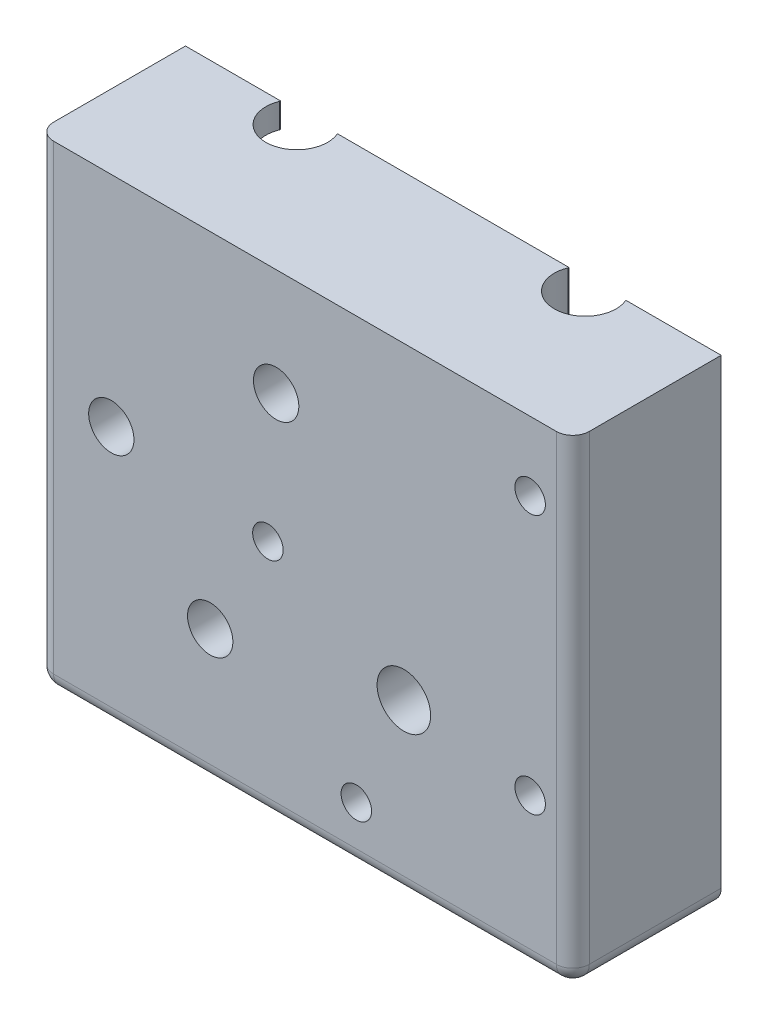
SolidWorks part; units mm, degrees
ref_plane "Front Plane" through (0, 0, 0) normal (0, 0, 1) x (1, 0, 0)
ref_plane "Top Plane" through (0, 0, 0) normal (0, 1, 0) x (1, 0, 0)
ref_plane "Right Plane" through (0, 0, 0) normal (1, 0, 0) x (0, 0, -1)
sketch "Sketch1" plane through (0, 0, 0) normal (0, 0, 1) x (1, 0, 0)
  line L28 (-44.5, 34.5) -> (-32.9789, 34.5)
  line L29 (-32.9789, 34.5) -> (-32.9789, 37.5)
  line L30 (-32.9789, 37.5) -> (-44.5, 37.5)
  line L31 (-44.5, 37.5) -> (-44.5, 34.5)
  line L32 (-26.0211, 30.5) -> (-26.0211, 5.4298)
  line L33 (-14.9652, 0.9641) -> (-7.0998, -1.4681)
  line L34 (-0.1869, 7.2476) -> (-7.1051, 19.0663)
  line L35 (-23.5, 30.5) -> (-26.0211, 30.5)
  line L36 (-26.0211, 37.5) -> (-26.0211, 34.5)
  line L37 (-26.0211, 34.5) -> (-15.5, 34.5)
  line L38 (-5.686, 22.5805) -> (2.0211, 9.414)
  line L39 (2.0211, 9.414) -> (2.0211, 37.5)
  line L40 (2.0211, 37.5) -> (-26.0211, 37.5)
  line L41 (8.9789, 37.5) -> (8.9789, -20.5)
  line L42 (8.9789, -20.5) -> (18.5, -20.5)
  line L43 (20.5, -18.5) -> (20.5, 37.5)
  line L44 (20.5, 37.5) -> (8.9789, 37.5)
  line L45 (-26.0211, -14.2471) -> (-26.0211, -20.5)
  line L46 (-26.0211, -20.5) -> (2.0211, -20.5)
  line L47 (2.0211, -20.5) -> (2.0211, -6.9626)
  line L48 (-4.9882, -5.2612) -> (-13.6389, -2.5862)
  line L49 (-23.5, -14.2471) -> (-26.0211, -14.2471)
  line L50 (-32.9789, 12.0984) -> (-32.9789, 30.5)
  line L51 (-32.9789, 30.5) -> (-44.5, 30.5)
  line L52 (-44.5, 30.5) -> (-44.5, -18.5)
  line L53 (-42.5, -20.5) -> (-32.9789, -20.5)
  line L54 (-32.9789, -20.5) -> (-32.9789, -7.4332)
  line L55 (-32.9789, -1.0611) -> (-32.9789, 9.9016)
  arc A16 (-14.9652, 0.9641) -> (-26.0211, 5.4298) centre (-23.5, -4.2471) ccw
  arc A17 (-0.1869, 7.2476) -> (-7.0998, -1.4681) centre (0, 0) ccw
  arc A18 (-12.5519, 14.9444) -> (-7.1051, 19.0663) centre (-15.5, 24.5) ccw
  arc A19 (-18.4481, 14.9444) -> (-12.5519, 14.9444) centre (-15.5, 15.5) ccw
  arc A20 (-23.5, 30.5) -> (-18.4481, 14.9444) centre (-15.5, 24.5) ccw
  arc A21 (-5.686, 22.5805) -> (-15.5, 34.5) centre (-15.5, 24.5) ccw
  arc A22 (18.5, -20.5) -> (20.5, -18.5) centre (18.5, -18.5) ccw
  arc A23 (-4.9882, -5.2612) -> (2.0211, -6.9626) centre (0, 0) ccw
  arc A24 (-23.5, -14.2471) -> (-13.6389, -2.5862) centre (-23.5, -4.2471) ccw
  arc A25 (-44.5, -18.5) -> (-42.5, -20.5) centre (-42.5, -18.5) ccw
  arc A26 (-32.9789, -1.0611) -> (-32.9789, -7.4332) centre (-23.5, -4.2471) ccw
  arc A27 (-32.9789, 12.0984) -> (-32.9789, 9.9016) centre (-35.5, 11) ccw
  circle A28 centre (-5.7708, -13.6227) radius 1.85
  circle A29 centre (-10.7623, 8.4364) radius 1.85
  circle A30 centre (15.3222, 29.1269) radius 1.85
  circle A31 centre (15.3222, -2.3516) radius 1.85
extrude "Boss-Extrude1" add sketch "Sketch1" along normal blind 10
sketch "Sketch2" plane through (0, 0, 10) normal (0, 0, 1) x (1, 0, 0)
  circle A0 centre (-35.5, 11) radius 10
  dimension "D1" = 20
extrude "Cut-Extrude1" cut sketch "Sketch2" against normal through all
sketch "Sketch3" plane through (0, 0, 10) normal (0, 0, 1) x (1, 0, 0)
  line L0 (-32.9789, 20.677) -> (-32.9789, 30.5)
  line L1 (-32.9789, 30.5) -> (-44.5, 30.5)
  line L2 (-44.5, 30.5) -> (-44.5, 34.5)
  line L3 (-44.5, 34.5) -> (-32.9789, 34.5)
  line L4 (-32.9789, 34.5) -> (-32.9789, 37.5)
  line L5 (-32.9789, 37.5) -> (-26.0211, 37.5)
  line L6 (-26.0211, 37.5) -> (-26.0211, 34.5)
  line L7 (-26.0211, 34.5) -> (-15.5, 34.5)
  line L8 (-23.5, 30.5) -> (-26.0211, 30.5)
  line L9 (-26.0211, 30.5) -> (-26.0211, 14.1861)
  line L10 (8.9789, -20.5) -> (8.9789, 37.5)
  line L11 (8.9789, 37.5) -> (2.0211, 37.5)
  line L12 (2.0211, 37.5) -> (2.0211, 9.414)
  line L13 (2.0211, 9.414) -> (-5.686, 22.5805)
  line L14 (-7.1051, 19.0663) -> (-0.1869, 7.2476)
  line L15 (2.0211, -6.9626) -> (2.0211, -20.5)
  line L16 (2.0211, -20.5) -> (8.9789, -20.5)
  line L17 (-23.5, -14.2471) -> (-26.0211, -14.2471)
  line L18 (-26.0211, -14.2471) -> (-26.0211, -20.5)
  line L19 (-26.0211, -20.5) -> (-32.9789, -20.5)
  line L20 (-32.9789, -20.5) -> (-32.9789, -7.4332)
  line L21 (-26.0211, 7.8139) -> (-26.0211, 5.4298)
  line L22 (-32.9789, -1.0611) -> (-32.9789, 1.323)
  line L24 (-7.0998, -1.4681) -> (-14.9652, 0.9641)
  line L25 (-13.6389, -2.5862) -> (-4.9882, -5.2612)
  arc A6 (-12.5519, 14.9444) -> (-7.1051, 19.0663) centre (-15.5, 24.5) ccw
  arc A7 (-4.9882, -5.2612) -> (2.0211, -6.9626) centre (0, 0) ccw
  arc A8 (-23.5, -14.2471) -> (-13.6389, -2.5862) centre (-23.5, -4.2471) ccw
  arc A9 (-32.9789, 1.323) -> (-26.0211, 7.8139) centre (-35.5, 11) ccw
  arc A10 (-14.9652, 0.9641) -> (-26.0211, 5.4298) centre (-23.5, -4.2471) ccw
  arc A12 (-0.1869, 7.2476) -> (-7.0998, -1.4681) centre (0, 0) ccw
  arc A13 (-32.9789, -1.0611) -> (-32.9789, -7.4332) centre (-23.5, -4.2471) ccw
  arc A14 (-18.4481, 14.9444) -> (-12.5519, 14.9444) centre (-15.5, 15.5) ccw
  arc A15 (-5.686, 22.5805) -> (-15.5, 34.5) centre (-15.5, 24.5) ccw
  arc A16 (-23.5, 30.5) -> (-18.4481, 14.9444) centre (-15.5, 24.5) ccw
  arc A17 (-26.0211, 14.1861) -> (-32.9789, 20.677) centre (-35.5, 11) ccw
  circle A18 centre (0, 0) radius 3.25
  dimension "D1" = 6.5
extrude "Boss-Extrude2" add sketch "Sketch3" against normal blind 7.5
sketch "Sketch4" plane through (0, 0, 10) normal (0, 0, 1) x (1, 0, 0)
  line L0 (-44.5, 6.6411) -> (-44.5, -18.5)
  line L1 (-44.5, 37.5) -> (20.5, 37.5)
  line L2 (-44.5, 37.5) -> (-44.5, 15.3589)
  line L3 (-42.5, -20.5) -> (18.5, -20.5)
  line L4 (20.5, 37.5) -> (20.5, -18.5)
  arc A0 (-44.5, 6.6411) -> (-44.5, 15.3589) centre (-35.5, 11) ccw
  circle A1 centre (-10.7623, 8.4364) radius 1.85
  circle A2 centre (0, 0) radius 3.25
  circle A3 centre (-5.7708, -13.6227) radius 1.85
  circle A4 centre (15.3222, -2.3516) radius 1.85
  circle A5 centre (15.3222, 29.1269) radius 1.85
  arc A6 (-44.5, -18.5) -> (-42.5, -20.5) centre (-42.5, -18.5) ccw
  arc A7 (18.5, -20.5) -> (20.5, -18.5) centre (18.5, -18.5) ccw
extrude "Boss-Extrude3" add sketch "Sketch4" along normal blind 2
sketch "Sketch5" plane through (0, 0, 12) normal (0, 0, 1) x (1, 0, 0)
  line L1 (-44.5, 37.5) -> (20.5, 37.5)
  line L2 (-44.5, 37.5) -> (-44.5, -18.5)
  line L3 (-42.5, -20.5) -> (18.5, -20.5)
  line L4 (20.5, 37.5) -> (20.5, -18.5)
  arc A0 (-44.5, -18.5) -> (-42.5, -20.5) centre (-42.5, -18.5) ccw
  arc A1 (18.5, -20.5) -> (20.5, -18.5) centre (18.5, -18.5) ccw
  circle A2 centre (0, 0) radius 3.25
  circle A3 centre (-10.7623, 8.4364) radius 1.85
  circle A4 centre (15.3222, 29.1269) radius 1.85
  circle A5 centre (15.3222, -2.3516) radius 1.85
  circle A6 centre (-5.7708, -13.6227) radius 1.85
extrude "Boss-Extrude4" add sketch "Sketch5" along normal blind 6
fillet "Fillet1" radius 2 5 edges at (20.5, 9.5, 18) (19.9142, -19.9142, 18) (-12, -20.5, 18) (-43.9142, -19.9142, 18) (-44.5, 9.5, 18)
sketch "Sketch6" plane through (0, 0, 0) normal (0, 0, -1) x (-1, 0, 0)
  line L0 (44.5, 6.6411) -> (44.5, -18.5) construction
  line L1 (35.5, 21) -> (44.5, 21)
  line L2 (35.5, 21) -> (35.5, 1)
  line L3 (35.5, 1) -> (44.5, 1)
  line L4 (44.5, 21) -> (44.5, 1)
  arc A0 (44.5, 15.3589) -> (44.5, 6.6411) centre (35.5, 11) ccw construction
  arc A1 (44.5, 15.3589) -> (32.9789, 20.677) centre (35.5, 11) ccw construction
extrude "Cut-Extrude2" cut sketch "Sketch6" against normal up to surface (12 mm away) up to face at (-35, 11, 12)
sketch "Sketch7" plane through (0, 0, 2.5) normal (0, 0, -1) x (-1, 0, 0)
  line L0 (32.9789, -20.5) -> (26.0211, -20.5) construction
  line L1 (28.0011, -20.5) -> (30.9989, -20.5)
  line L2 (28.0011, -20.5) -> (28.0011, 9.1226)
  line L3 (28.0011, 9.1226) -> (30.9989, 9.1226)
  line L4 (30.9989, -20.5) -> (30.9989, 9.1226)
  line L5 (26.0211, -14.2471) -> (26.0211, -20.5) construction
  line L6 (32.9789, -20.5) -> (32.9789, -7.4332) construction
  dimension "D1" = 1.98
  dimension "D2" = 1.98
extrude "Cut-Extrude3" cut sketch "Sketch7" against normal up to surface (9.5 mm away) up to face at (-37.5, 11, 12)
sketch "Sketch8" plane through (0, 0, 12) normal (0, 0, -1) x (-1, 0, 0)
  circle A0 centre (35.5, 11) radius 2.75
  dimension "D1" = 5.5
extrude "Cut-Extrude4" cut sketch "Sketch8" against normal blind 6
sketch "Sketch9" plane through (0, 0, 2.5) normal (0, 0, -1) x (-1, 0, 0)
  circle A0 centre (15.5, 24.5) radius 2.75
  circle A1 centre (23.5, -4.2471) radius 2.75
  dimension "D1" = 5.5
  dimension "D2" = 5.5
extrude "Cut-Extrude5" cut sketch "Sketch9" against normal through all
sketch "Sketch10" plane through (0, 0, 18) normal (0, 0, 1) x (1, 0, 0)
  line L1 (20.5, 37.5) -> (20.5, -18.5) construction
  circle A0 centre (-16.5, 8.4364) radius 1.85
  dimension "D1" = 37
  dimension "D2" = 3.7
extrude "Cut-Extrude6" cut sketch "Sketch10" against normal blind 25
sketch "Sketch11" plane through (0, 0, 18) normal (0, 0, 1) x (1, 0, 0)
  circle A0 centre (-10.7623, 8.4364) radius 1.85
extrude "Boss-Extrude5" add sketch "Sketch11" against normal through all
sketch "Sketch12" plane through (0, -20.5, 0) normal (0, -1, 0) x (1, 0, 0)
  line L0 (-26.0211, 0) -> (2.0211, 0) construction
  line L1 (-32.9789, 2.5) -> (-32.9789, 0) construction
  line L2 (-26.0211, 2.5) -> (-26.0211, 0) construction
  line L3 (8.9789, 2.5) -> (8.9789, 0) construction
  circle A0 centre (-29.4989, 1.5) radius 3.75
  circle A1 centre (5.4989, 1.5) radius 3.75
  dimension "D1" = 7.5
  dimension "D2" = 1.5
  dimension "D3" = 7.5
  dimension "D4" = 1.5
  dimension "D5" = 3.48
  dimension "D6" = 3.4777
  dimension "D7" = 3.48
extrude "Cut-Extrude7" cut sketch "Sketch12" against normal through all
sketch "Sketch13" plane through (0, 0, 2.5) normal (0, 0, -1) x (-1, 0, 0)
  circle A0 centre (0, 0) radius 7.5
  dimension "D1" = 15
extrude "Cut-Extrude8" cut sketch "Sketch13" against normal blind 10
